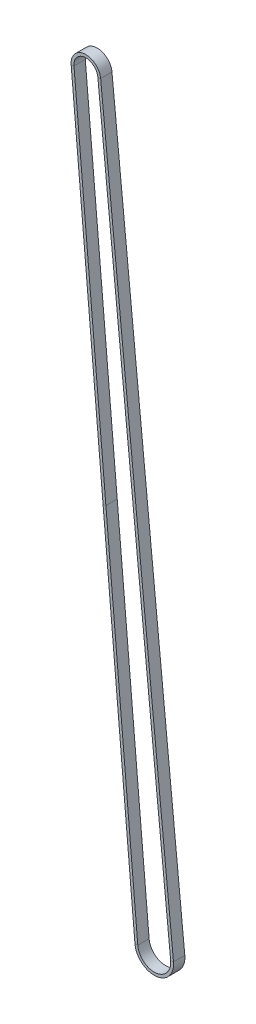
SolidWorks part; units mm, degrees
material "POLYURETHANE (11671)"
ref_plane "Front Plane" through (0, 0, 0) normal (0, 0, 1) x (1, 0, 0)
ref_plane "Top Plane" through (0, 0, 0) normal (0, 1, 0) x (1, 0, 0)
ref_plane "Right Plane" through (0, 0, 0) normal (1, 0, 0) x (0, 0, -1)
sketch "Sketch1" plane through (0, 0, 0) normal (0, 0, 1) x (1, 0, 0)
  line L0 (-42.5298, 385.7613) -> (-8.7167, -0.7625)
  line L1 (-29.8854, 386.9463) -> (8.7066, 0.8703)
  arc A2 (-29.8854, 386.9463) -> (-42.5298, 385.7613) centre (-36.2039, 386.3147) ccw
  arc A3 (-8.7167, -0.7625) -> (8.7066, 0.8703) centre (0, 0) ccw
  circle A4 centre (0, 0) radius 8.75 construction
  circle A5 centre (-36.2039, 386.3147) radius 6.35 construction
  point P4 (-25.6232, 192.4994)
ref_plane "Plane1" through (-25.6232, 192.4994, 0) normal (0.0871, -0.9962, 0) x (-0.9962, -0.0871, 0)
sketch "Sketch2" plane through (-25.6232, 192.4994, 0) normal (0.0871, -0.9962, 0) x (-0.9962, -0.0871, 0)
  line L1 (1.5, 3) -> (0, 3)
  line L2 (1.5, 3) -> (1.5, -3)
  line L3 (1.5, -3) -> (0, -3)
  line L4 (0, 3) -> (0, -3)
  point P4 (0, 0)
  dimension "D1" = 1.5
  dimension "D2" = 6
sweep "Sweep1" add profiles "Sketch2" path "Sketch1"
